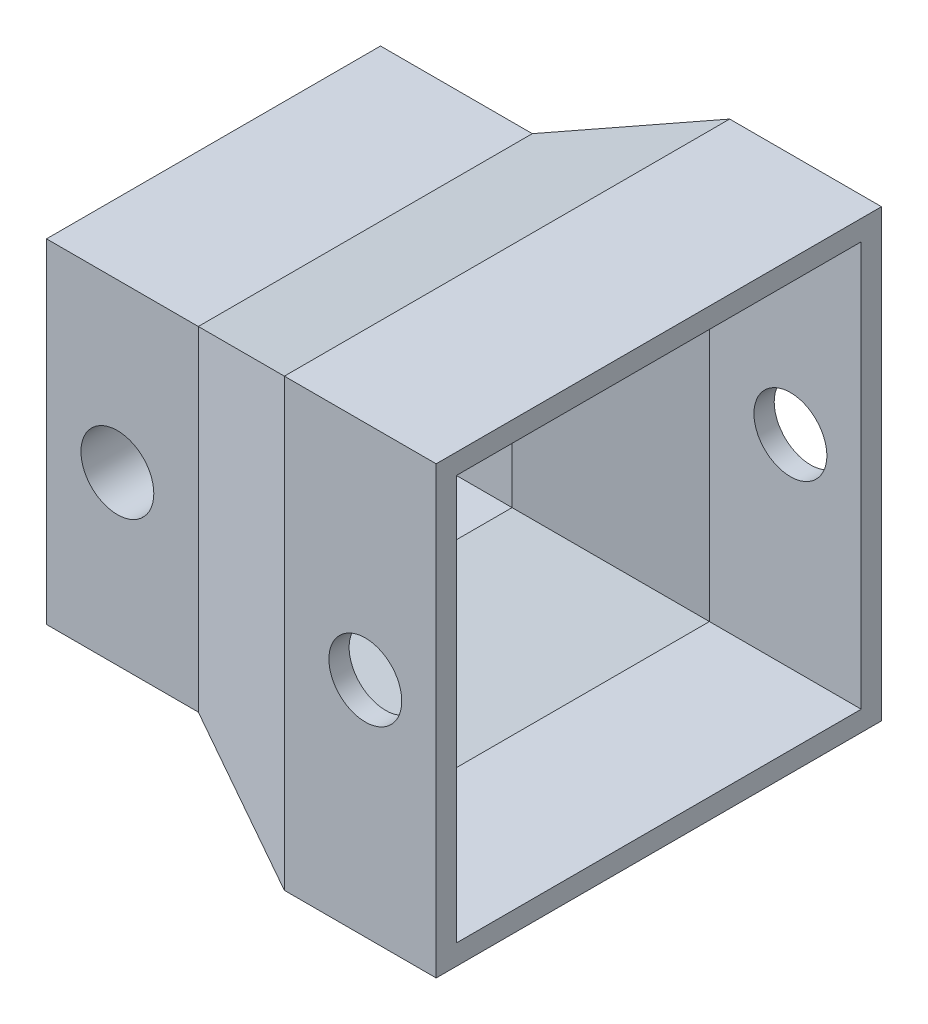
SolidWorks part; units mm, degrees
ref_plane "正面" through (0, 0, 0) normal (0, 0, 1) x (1, 0, 0)
ref_plane "平面" through (0, 0, 0) normal (0, 1, 0) x (1, 0, 0)
ref_plane "右側面" through (0, 0, 0) normal (1, 0, 0) x (0, 0, -1)
sketch "ｽｹｯﾁ1" plane through (0, 0, 0) normal (0, 0, 1) x (1, 0, 0)
  circle A0 centre (0, 0) radius 2.5
  dimension "D1" = 5
extrude "ﾎﾞｽ - 押し出し1" add sketch "ｽｹｯﾁ1" along normal blind 1.5
sketch "ｽｹｯﾁ2" plane through (0, 0, 1.5) normal (0, 0, 1) x (1, 0, 0)
  circle A0 centre (0, 0) radius 3.5
  dimension "D1" = 7
extrude "ﾎﾞｽ - 押し出し2" add sketch "ｽｹｯﾁ2" along normal blind 1
sketch "ｽｹｯﾁ3" plane through (0, 0, 2.5) normal (0, 0, 1) x (1, 0, 0)
  circle A0 centre (0, 0) radius 2.5 construction
  circle A1 centre (0, 0) radius 2.5
extrude "ﾎﾞｽ - 押し出し3" add sketch "ｽｹｯﾁ3" along normal blind 2.5
sketch "ｽｹｯﾁ4" plane through (0, 0, 5) normal (0, 0, 1) x (1, 0, 0)
  circle A1 centre (0, 0) radius 3.5
  circle A2 centre (0, 0) radius 3.5
  dimension "D1" = 0
extrude "ﾎﾞｽ - 押し出し4" add sketch "ｽｹｯﾁ4" along normal blind 1
sketch "ｽｹｯﾁ5" plane through (0, 0, 6) normal (0, 0, 1) x (1, 0, 0)
  circle A0 centre (0, 0) radius 2.5 construction
  circle A1 centre (0, 0) radius 2.5
extrude "ﾎﾞｽ - 押し出し5" add sketch "ｽｹｯﾁ5" along normal blind 2.5
sketch "ｽｹｯﾁ6" plane through (0, 0, 8.5) normal (0, 0, 1) x (1, 0, 0)
  circle A1 centre (0, 0) radius 3.5
  circle A2 centre (0, 0) radius 3.5
  dimension "D1" = 0
extrude "ﾎﾞｽ - 押し出し6" add sketch "ｽｹｯﾁ6" along normal blind 1
sketch "ｽｹｯﾁ7" plane through (0, 0, 9.5) normal (0, 0, 1) x (1, 0, 0)
  circle A0 centre (0, 0) radius 2.5 construction
  circle A1 centre (0, 0) radius 2.5
extrude "ﾎﾞｽ - 押し出し7" add sketch "ｽｹｯﾁ7" along normal blind 2.5
sketch "ｽｹｯﾁ10" plane through (0, 0, 12) normal (0, 0, 1) x (1, 0, 0)
  circle A1 centre (0, 0) radius 3.5
  circle A2 centre (0, 0) radius 3.5
  dimension "D1" = 0
extrude "ﾎﾞｽ - 押し出し9" add sketch "ｽｹｯﾁ10" along normal blind 1
sketch "ｽｹｯﾁ11" plane through (0, 0, 13) normal (0, 0, 1) x (1, 0, 0)
  circle A0 centre (0, 0) radius 2.5 construction
  circle A1 centre (0, 0) radius 2.5
extrude "ﾎﾞｽ - 押し出し10" add sketch "ｽｹｯﾁ11" along normal blind 1.5
sketch "ｽｹｯﾁ12" plane through (0, 0, 14.5) normal (0, 0, 1) x (1, 0, 0)
  circle A0 centre (0, 0) radius 1.8
  dimension "D1" = 3.6
extrude "ｶｯﾄ - 押し出し2" cut sketch "ｽｹｯﾁ12" against normal through all
ref_plane "平面1" through (15, 0, 0) normal (1, 0, 0) x (0, 0, -1)
sketch "ｽｹｯﾁ13" plane through (15, 0, 0) normal (1, 0, 0) x (0, 0, -1)
  line L0 (0, 0) -> (-7.25, 0) construction
  line L1 (-18.25, -11) -> (3.75, -11)
  line L2 (-18.25, -11) -> (-18.25, 11)
  line L3 (-18.25, 11) -> (3.75, 11)
  line L4 (3.75, -11) -> (3.75, 11)
  line L5 (-18.25, -11) -> (3.75, 11) construction
  line L6 (-18.25, 11) -> (3.75, -11) construction
  line L7 (-7.25, 0) -> (-14.5, 0) construction
  line L8 (-14.5, 2.5) -> (-14.5, -2.5) construction
  line L10 (2.75, -10) -> (-17.25, -10)
  line L11 (2.75, -10) -> (2.75, 10)
  line L12 (2.75, 10) -> (-17.25, 10)
  line L13 (-17.25, -10) -> (-17.25, 10)
  line L14 (2.75, -10) -> (-17.25, 10) construction
  line L15 (2.75, 10) -> (-17.25, -10) construction
  point P4 (-7.25, 0)
  dimension "D1" = 22
  dimension "D2" = 22
  dimension "D3" = 1
extrude "ﾎﾞｽ - 押し出し11" add sketch "ｽｹｯﾁ13" along normal blind 3.5 and the other way blind 4 separate body
sketch "ｽｹｯﾁ14" plane through (0, 0, 0) normal (1, 0, 0) x (0, 0, -1)
  line L0 (-18.25, 11) -> (3.75, -11) construction
  line L1 (1, -8.25) -> (-15.5, -8.25)
  line L2 (1, -8.25) -> (1, 8.25)
  line L3 (1, 8.25) -> (-15.5, 8.25)
  line L4 (-15.5, -8.25) -> (-15.5, 8.25)
  line L5 (1, -8.25) -> (-15.5, 8.25) construction
  line L6 (1, 8.25) -> (-15.5, -8.25) construction
  line L7 (-14.5, 2.5) -> (-14.5, -2.5) construction
  line L8 (0, -7.25) -> (-14.5, -7.25)
  line L9 (0, -7.25) -> (0, 7.25)
  line L10 (0, 7.25) -> (-14.5, 7.25)
  line L11 (-14.5, -7.25) -> (-14.5, 7.25)
  line L12 (0, -7.25) -> (-14.5, 7.25) construction
  line L13 (0, 7.25) -> (-14.5, -7.25) construction
  point P0 (-7.25, 0)
  point P9 (-7.25, 0)
  dimension "D1" = 1
extrude "ﾎﾞｽ - 押し出し12" add sketch "ｽｹｯﾁ14" along normal blind 4 and the other way blind 3.5
sketch "ｽｹｯﾁ16" plane through (11, 0, 0) normal (-1, 0, 0) x (0, 0, 1)
  line L0 (-3.75, 11) -> (-2.75, 10)
  line L1 (-2.75, 10) -> (17.25, 10)
  line L2 (17.25, 10) -> (18.25, 11)
  line L3 (18.25, 11) -> (-3.75, 11)
sketch "ｽｹｯﾁ17" plane through (4, 0, 0) normal (1, 0, 0) x (0, 0, -1)
  line L0 (-15.5, 8.25) -> (-14.5, 7.25)
  line L1 (-14.5, 7.25) -> (0, 7.25)
  line L2 (0, 7.25) -> (1, 8.25)
  line L3 (1, 8.25) -> (-15.5, 8.25)
loft "ﾛﾌﾄ2" add profiles "ｽｹｯﾁ16", "ｽｹｯﾁ17"
sketch "ｽｹｯﾁ18" plane through (0, 0, 0) normal (0, 1, 0) x (1, 0, 0)
  line L0 (0.25, 1) -> (0.25, -15.5)
  line L1 (-3.5, 1) -> (4, 1) construction
  line L2 (-3.5, -15.5) -> (4, -15.5) construction
  line L3 (0.25, -7.25) -> (-9.75, -7.25)
  dimension "D1" = 10
pattern_circular "円形ﾊﾟﾀｰﾝ1" count 4 over 360 about axis through (0, 0, 7.25) along (1, 0, 0) of "ﾛﾌﾄ2"
sketch "ｽｹｯﾁ19" plane through (0, 0, 15.5) normal (0, 0, 1) x (1, 0, 0)
  circle A1 centre (0, 0) radius 1.8
  circle A2 centre (0, 0) radius 1.8
  dimension "D1" = 0
extrude "ｶｯﾄ - 押し出し3" cut sketch "ｽｹｯﾁ19" against normal through all
sketch "ｽｹｯﾁ20" plane through (0, 0, 18.25) normal (0, 0, 1) x (1, 0, 0)
  line L0 (15, -3.85) -> (15, 3.85) construction
  line L1 (0, 0) -> (15, 0) construction
  circle A0 centre (15, 0) radius 1.8
  dimension "D1" = 3.6
extrude "ｶｯﾄ - 押し出し4" cut sketch "ｽｹｯﾁ20" against normal through all
